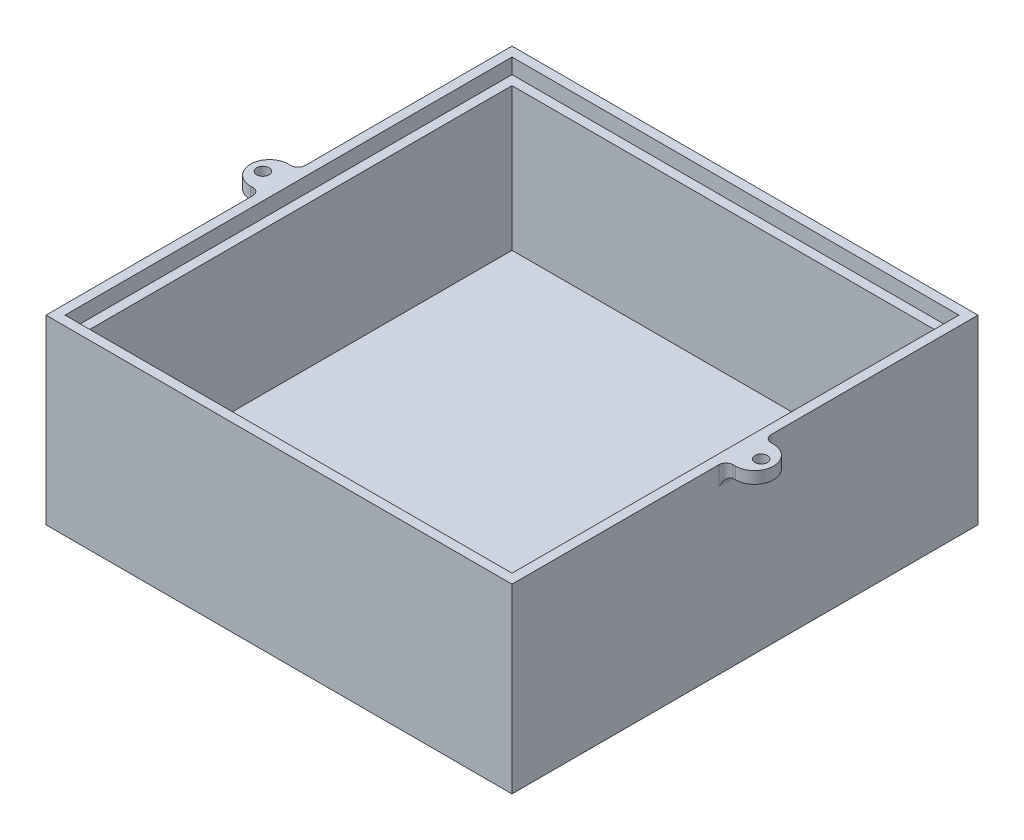
SolidWorks part; units mm, degrees
ref_plane "Front Plane" through (0, 0, 0) normal (0, 0, 1) x (1, 0, 0)
ref_plane "Top Plane" through (0, 0, 0) normal (0, 1, 0) x (1, 0, 0)
ref_plane "Right Plane" through (0, 0, 0) normal (1, 0, 0) x (0, 0, -1)
sketch "Sketch1" plane through (0, 0, 0) normal (0, 1, 0) x (1, 0, 0)
  line L1 (-49, 49) -> (49, 49)
  line L2 (-49, 49) -> (-49, -49)
  line L3 (-49, -49) -> (49, -49)
  line L4 (49, 49) -> (49, -49)
  line L5 (-49, 49) -> (49, -49) construction
  line L6 (-49, -49) -> (49, 49) construction
  point P0 (0, 0)
  dimension "D1" = 98
  dimension "D2" = 98
extrude "Boss-Extrude1" add sketch "Sketch1" along normal blind 40
sketch "Sketch2" plane through (0, 40, 0) normal (0, 1, 0) x (1, 0, 0)
  line L1 (-47, 47) -> (47, 47)
  line L2 (-47, 47) -> (-47, -47)
  line L3 (-47, -47) -> (47, -47)
  line L4 (47, 47) -> (47, -47)
  line L5 (-47, 47) -> (47, -47) construction
  line L6 (-47, -47) -> (47, 47) construction
  point P0 (0, 0)
  dimension "D1" = 94
  dimension "D2" = 94
extrude "Cut-Extrude1" cut sketch "Sketch2" against normal blind 5
sketch "Sketch3" plane through (0, 35, 0) normal (0, 1, 0) x (1, 0, 0)
  line L1 (-45, 45) -> (45, 45)
  line L2 (-45, 45) -> (-45, -45)
  line L3 (-45, -45) -> (45, -45)
  line L4 (45, 45) -> (45, -45)
  line L5 (-45, 45) -> (45, -45) construction
  line L6 (-45, -45) -> (45, 45) construction
  point P0 (0, 0)
  dimension "D1" = 90
  dimension "D2" = 90
extrude "Cut-Extrude2" cut sketch "Sketch3" against normal blind 30
sketch "Sketch4" plane through (0, 40, 0) normal (0, 1, 0) x (1, 0, 0)
  line L1 (-47, 47) -> (47, 47)
  line L2 (-47, 47) -> (-47, -47)
  line L3 (-47, -47) -> (47, -47)
  line L4 (47, 47) -> (47, -47)
  line L5 (-49, 49) -> (49, 49)
  line L6 (-49, 49) -> (-49, -49)
  line L7 (-49, -49) -> (49, -49)
  line L8 (49, 49) -> (49, -49)
extrude "Cut-Extrude3" cut sketch "Sketch4" against normal blind 1.8
sketch "Sketch5" plane through (0, 38.2, 0) normal (0, 1, 0) x (1, 0, 0)
  line L0 (-49, 49) -> (-49, -49) construction
  line L1 (-49, 4) -> (-51, 4)
  line L2 (-49, 4) -> (-49, -4)
  line L3 (-49, -4) -> (-51, -4)
  line L5 (49, 49) -> (-49, 49) construction
  line L7 (0, -8.1636) -> (0, 15.1829) construction
  line L8 (49, 4) -> (49, -4)
  line L9 (49, -4) -> (51, -4)
  line L10 (49, 4) -> (51, 4)
  arc A0 (-51, 4) -> (-51, -4) centre (-51, 0) ccw
  circle A1 centre (-52.4, 0) radius 1.3
  circle A2 centre (52.4, 0) radius 1.3
  arc A3 (51, 4) -> (51, -4) centre (51, 0) cw
  dimension "D4" = 2.6
  dimension "D1" = 2
  dimension "D2" = 8
  dimension "D3" = 45
  dimension "D5" = 3.4
extrude "Boss-Extrude2" add sketch "Sketch5" against normal blind 2.5
fillet "Fillet1" radius 1.5 3 edges at (-49, 36.95, -4) (-49, 35.7, 0) (-49, 36.95, 4)
fillet "Fillet2" radius 1.5 3 edges at (49, 36.95, -4) (49, 35.7, 0) (49, 36.95, 4)
